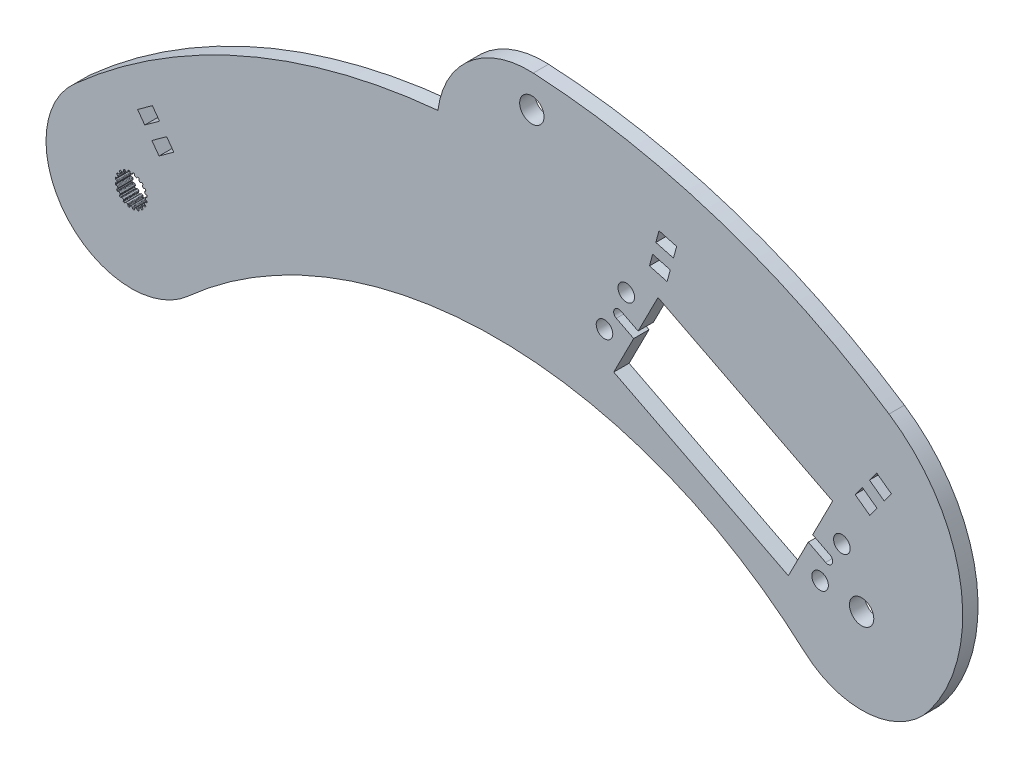
SolidWorks part; units mm, degrees
ref_plane "Front Plane" through (0, 0, 0) normal (0, 0, 1) x (1, 0, 0)
ref_plane "Top Plane" through (0, 0, 0) normal (0, 1, 0) x (1, 0, 0)
ref_plane "Right Plane" through (0, 0, 0) normal (1, 0, 0) x (0, 0, -1)
sketch "Sketch1" plane through (0, 0, 0) normal (0, 0, 1) x (1, 0, 0)
  line L0 (-0.1069, 2.9699) -> (0.1069, 2.9699)
  line L1 (0.3159, 3.2375) -> (0.2537, 3.0575)
  line L2 (-0.2964, 3.2367) -> (-0.2318, 3.0575)
  line L3 (-0.2964, 3.2367) -> (0.3159, 3.2375) construction
  line L4 (0, 3.3252) -> (0, 0) construction
  line L5 (-0.2318, 3.0575) -> (0.2537, 3.0575) construction
  line L6 (-0.4281, 3.3241) -> (0.4281, 3.3263) construction
  line L7 (0.7183, 3.1698) -> (0.7244, 2.9795)
  line L8 (0.816, 2.8576) -> (1.0195, 2.7915)
  line L9 (1.3009, 2.9815) -> (1.1862, 2.8295)
  line L10 (1.6627, 2.7927) -> (1.6097, 2.6099)
  line L11 (1.6591, 2.4655) -> (1.8322, 2.3398)
  line L12 (2.1585, 2.4335) -> (2.0025, 2.3245)
  line L13 (2.4443, 2.1423) -> (2.3374, 1.9847)
  line L14 (2.3398, 1.8322) -> (2.4655, 1.6591)
  line L15 (2.8049, 1.6474) -> (2.6228, 1.5919)
  line L16 (2.9866, 1.2821) -> (2.8363, 1.1653)
  line L17 (2.7915, 1.0195) -> (2.8576, 0.816)
  line L18 (3.1767, 0.7) -> (2.9863, 0.7035)
  line L19 (3.2367, 0.2964) -> (3.0575, 0.2318)
  line L20 (2.9699, 0.1069) -> (2.9699, -0.1069)
  line L21 (3.2375, -0.3159) -> (3.0575, -0.2537)
  line L22 (3.1698, -0.7183) -> (2.9795, -0.7244)
  line L23 (2.8576, -0.816) -> (2.7915, -1.0195)
  line L24 (2.9815, -1.3009) -> (2.8295, -1.1862)
  line L25 (2.7927, -1.6627) -> (2.6099, -1.6097)
  line L26 (2.4655, -1.6591) -> (2.3398, -1.8322)
  line L27 (2.4335, -2.1585) -> (2.3245, -2.0025)
  line L28 (2.1423, -2.4443) -> (1.9847, -2.3374)
  line L29 (1.8322, -2.3398) -> (1.6591, -2.4655)
  line L30 (1.6474, -2.8049) -> (1.5919, -2.6228)
  line L31 (1.2821, -2.9866) -> (1.1653, -2.8363)
  line L32 (1.0195, -2.7915) -> (0.816, -2.8576)
  line L33 (0.7, -3.1767) -> (0.7035, -2.9863)
  line L34 (0.2964, -3.2367) -> (0.2318, -3.0575)
  line L35 (0.1069, -2.9699) -> (-0.1069, -2.9699)
  line L36 (-0.3159, -3.2375) -> (-0.2537, -3.0575)
  line L37 (-0.7183, -3.1698) -> (-0.7244, -2.9795)
  line L38 (-0.816, -2.8576) -> (-1.0195, -2.7915)
  line L39 (-1.3009, -2.9815) -> (-1.1862, -2.8295)
  line L40 (-1.6627, -2.7927) -> (-1.6097, -2.6099)
  line L41 (-1.6591, -2.4655) -> (-1.8322, -2.3398)
  line L42 (-2.1585, -2.4335) -> (-2.0025, -2.3245)
  line L43 (-2.4443, -2.1423) -> (-2.3374, -1.9847)
  line L44 (-2.3398, -1.8322) -> (-2.4655, -1.6591)
  line L45 (-2.8049, -1.6474) -> (-2.6228, -1.5919)
  line L46 (-2.9866, -1.2821) -> (-2.8363, -1.1653)
  line L47 (-2.7915, -1.0195) -> (-2.8576, -0.816)
  line L48 (-3.1767, -0.7) -> (-2.9863, -0.7035)
  line L49 (-3.2367, -0.2964) -> (-3.0575, -0.2318)
  line L50 (-2.9699, -0.1069) -> (-2.9699, 0.1069)
  line L51 (-3.2375, 0.3159) -> (-3.0575, 0.2537)
  line L52 (-3.1698, 0.7183) -> (-2.9795, 0.7244)
  line L53 (-2.8576, 0.816) -> (-2.7915, 1.0195)
  line L54 (-2.9815, 1.3009) -> (-2.8295, 1.1862)
  line L55 (-2.7927, 1.6627) -> (-2.6099, 1.6097)
  line L56 (-2.4655, 1.6591) -> (-2.3398, 1.8322)
  line L57 (-2.4335, 2.1585) -> (-2.3245, 2.0025)
  line L58 (-2.1423, 2.4443) -> (-1.9847, 2.3374)
  line L59 (-1.8322, 2.3398) -> (-1.6591, 2.4655)
  line L60 (-1.6474, 2.8049) -> (-1.5919, 2.6228)
  line L61 (-1.2821, 2.9866) -> (-1.1653, 2.8363)
  line L62 (-1.0195, 2.7915) -> (-0.816, 2.8576)
  line L63 (-0.7, 3.1767) -> (-0.7035, 2.9863)
  line L64 (0.4281, 3.3263) -> (0.62, 3.2938)
  line L65 (1.4351, 3.0312) -> (1.6075, 2.9409)
  line L66 (2.3015, 2.4394) -> (2.4376, 2.3003)
  line L67 (2.9427, 1.6088) -> (3.0291, 1.4344)
  line L68 (3.2958, 0.6207) -> (3.3241, 0.4281)
  line L69 (3.3263, -0.4281) -> (3.2938, -0.62)
  line L70 (3.0312, -1.4351) -> (2.9409, -1.6075)
  line L71 (2.4394, -2.3015) -> (2.3003, -2.4376)
  line L72 (1.6088, -2.9427) -> (1.4344, -3.0291)
  line L73 (0.6207, -3.2958) -> (0.4281, -3.3241)
  line L74 (-0.4281, -3.3263) -> (-0.62, -3.2938)
  line L75 (-1.4351, -3.0312) -> (-1.6075, -2.9409)
  line L76 (-2.3015, -2.4394) -> (-2.4376, -2.3003)
  line L77 (-2.9427, -1.6088) -> (-3.0291, -1.4344)
  line L78 (-3.2958, -0.6207) -> (-3.3241, -0.4281)
  line L79 (-3.3263, 0.4281) -> (-3.2938, 0.62)
  line L80 (-3.0312, 1.4351) -> (-2.9409, 1.6075)
  line L81 (-2.4394, 2.3015) -> (-2.3003, 2.4376)
  line L82 (-1.6088, 2.9427) -> (-1.4344, 3.0291)
  line L83 (-0.6207, 3.2958) -> (-0.4281, 3.3241)
  line L84 (-11.8753, 13.2369) -> (11.8753, -13.2369) construction
  line L85 (164.2753, 13.2369) -> (140.5247, -13.2369) construction
  line L86 (0, 0) -> (152.4, 0) construction
  arc A0 (0.2537, 3.0575) -> (0.1069, 2.9699) centre (0.1283, 3.1009) cw
  arc A1 (-0.2318, 3.0575) -> (-0.1069, 2.9699) centre (-0.1069, 3.1026) ccw
  arc A2 (0.62, 3.2938) -> (0.7183, 3.1698) centre (0.5856, 3.1656) cw
  arc A3 (0.7244, 2.9795) -> (0.816, 2.8576) centre (0.857, 2.9838) ccw
  arc A4 (-0.4281, 3.3241) -> (-0.2964, 3.2367) centre (-0.4213, 3.1916) cw
  arc A5 (0.4281, 3.3263) -> (0.3159, 3.2375) centre (0.4413, 3.1942) ccw
  arc A6 (1.1862, 2.8295) -> (1.0195, 2.7915) centre (1.0802, 2.9095) cw
  arc A7 (1.4351, 3.0312) -> (1.3009, 2.9815) centre (1.4068, 2.9015) ccw
  arc A8 (1.6075, 2.9409) -> (1.6627, 2.7927) centre (1.5352, 2.8297) cw
  arc A9 (1.6097, 2.6099) -> (1.6591, 2.4655) centre (1.7371, 2.5729) ccw
  arc A10 (2.0025, 2.3245) -> (1.8322, 2.3398) centre (1.9264, 2.4332) cw
  arc A11 (2.3015, 2.4394) -> (2.1585, 2.4335) centre (2.2346, 2.3248) ccw
  arc A12 (2.4376, 2.3003) -> (2.4443, 2.1423) centre (2.3345, 2.2168) cw
  arc A13 (2.3374, 1.9847) -> (2.3398, 1.8322) centre (2.4472, 1.9102) ccw
  arc A14 (2.6228, 1.5919) -> (2.4655, 1.6591) centre (2.5841, 1.7189) cw
  arc A15 (2.9427, 1.6088) -> (2.8049, 1.6474) centre (2.8436, 1.5205) ccw
  arc A16 (3.0291, 1.4344) -> (2.9866, 1.2821) centre (2.9052, 1.3869) cw
  arc A17 (2.8363, 1.1653) -> (2.7915, 1.0195) centre (2.9177, 1.0605) ccw
  arc A18 (2.9863, 0.7035) -> (2.8576, 0.816) centre (2.9887, 0.8362) cw
  arc A19 (3.2958, 0.6207) -> (3.1767, 0.7) centre (3.1743, 0.5673) ccw
  arc A20 (3.3241, 0.4281) -> (3.2367, 0.2964) centre (3.1916, 0.4213) cw
  arc A21 (3.0575, 0.2318) -> (2.9699, 0.1069) centre (3.1026, 0.1069) ccw
  arc A22 (3.0575, -0.2537) -> (2.9699, -0.1069) centre (3.1009, -0.1283) cw
  arc A23 (3.3263, -0.4281) -> (3.2375, -0.3159) centre (3.1942, -0.4413) ccw
  arc A24 (3.2938, -0.62) -> (3.1698, -0.7183) centre (3.1656, -0.5856) cw
  arc A25 (2.9795, -0.7244) -> (2.8576, -0.816) centre (2.9838, -0.857) ccw
  arc A26 (2.8295, -1.1862) -> (2.7915, -1.0195) centre (2.9095, -1.0802) cw
  arc A27 (3.0312, -1.4351) -> (2.9815, -1.3009) centre (2.9015, -1.4068) ccw
  arc A28 (2.9409, -1.6075) -> (2.7927, -1.6627) centre (2.8297, -1.5352) cw
  arc A29 (2.6099, -1.6097) -> (2.4655, -1.6591) centre (2.5729, -1.7371) ccw
  arc A30 (2.3245, -2.0025) -> (2.3398, -1.8322) centre (2.4332, -1.9264) cw
  arc A31 (2.4394, -2.3015) -> (2.4335, -2.1585) centre (2.3248, -2.2346) ccw
  arc A32 (2.3003, -2.4376) -> (2.1423, -2.4443) centre (2.2168, -2.3345) cw
  arc A33 (1.9847, -2.3374) -> (1.8322, -2.3398) centre (1.9102, -2.4472) ccw
  arc A34 (1.5919, -2.6228) -> (1.6591, -2.4655) centre (1.7189, -2.5841) cw
  arc A35 (1.6088, -2.9427) -> (1.6474, -2.8049) centre (1.5205, -2.8436) ccw
  arc A36 (1.4344, -3.0291) -> (1.2821, -2.9866) centre (1.3869, -2.9052) cw
  arc A37 (1.1653, -2.8363) -> (1.0195, -2.7915) centre (1.0605, -2.9177) ccw
  arc A38 (0.7035, -2.9863) -> (0.816, -2.8576) centre (0.8362, -2.9887) cw
  arc A39 (0.6207, -3.2958) -> (0.7, -3.1767) centre (0.5673, -3.1743) ccw
  arc A40 (0.4281, -3.3241) -> (0.2964, -3.2367) centre (0.4213, -3.1916) cw
  arc A41 (0.2318, -3.0575) -> (0.1069, -2.9699) centre (0.1069, -3.1026) ccw
  arc A42 (-0.2537, -3.0575) -> (-0.1069, -2.9699) centre (-0.1283, -3.1009) cw
  arc A43 (-0.4281, -3.3263) -> (-0.3159, -3.2375) centre (-0.4413, -3.1942) ccw
  arc A44 (-0.62, -3.2938) -> (-0.7183, -3.1698) centre (-0.5856, -3.1656) cw
  arc A45 (-0.7244, -2.9795) -> (-0.816, -2.8576) centre (-0.857, -2.9838) ccw
  arc A46 (-1.1862, -2.8295) -> (-1.0195, -2.7915) centre (-1.0802, -2.9095) cw
  arc A47 (-1.4351, -3.0312) -> (-1.3009, -2.9815) centre (-1.4068, -2.9015) ccw
  arc A48 (-1.6075, -2.9409) -> (-1.6627, -2.7927) centre (-1.5352, -2.8297) cw
  arc A49 (-1.6097, -2.6099) -> (-1.6591, -2.4655) centre (-1.7371, -2.5729) ccw
  arc A50 (-2.0025, -2.3245) -> (-1.8322, -2.3398) centre (-1.9264, -2.4332) cw
  arc A51 (-2.3015, -2.4394) -> (-2.1585, -2.4335) centre (-2.2346, -2.3248) ccw
  arc A52 (-2.4376, -2.3003) -> (-2.4443, -2.1423) centre (-2.3345, -2.2168) cw
  arc A53 (-2.3374, -1.9847) -> (-2.3398, -1.8322) centre (-2.4472, -1.9102) ccw
  arc A54 (-2.6228, -1.5919) -> (-2.4655, -1.6591) centre (-2.5841, -1.7189) cw
  arc A55 (-2.9427, -1.6088) -> (-2.8049, -1.6474) centre (-2.8436, -1.5205) ccw
  arc A56 (-3.0291, -1.4344) -> (-2.9866, -1.2821) centre (-2.9052, -1.3869) cw
  arc A57 (-2.8363, -1.1653) -> (-2.7915, -1.0195) centre (-2.9177, -1.0605) ccw
  arc A58 (-2.9863, -0.7035) -> (-2.8576, -0.816) centre (-2.9887, -0.8362) cw
  arc A59 (-3.2958, -0.6207) -> (-3.1767, -0.7) centre (-3.1743, -0.5673) ccw
  arc A60 (-3.3241, -0.4281) -> (-3.2367, -0.2964) centre (-3.1916, -0.4213) cw
  arc A61 (-3.0575, -0.2318) -> (-2.9699, -0.1069) centre (-3.1026, -0.1069) ccw
  arc A62 (-3.0575, 0.2537) -> (-2.9699, 0.1069) centre (-3.1009, 0.1283) cw
  arc A63 (-3.3263, 0.4281) -> (-3.2375, 0.3159) centre (-3.1942, 0.4413) ccw
  arc A64 (-3.2938, 0.62) -> (-3.1698, 0.7183) centre (-3.1656, 0.5856) cw
  arc A65 (-2.9795, 0.7244) -> (-2.8576, 0.816) centre (-2.9838, 0.857) ccw
  arc A66 (-2.8295, 1.1862) -> (-2.7915, 1.0195) centre (-2.9095, 1.0802) cw
  arc A67 (-3.0312, 1.4351) -> (-2.9815, 1.3009) centre (-2.9015, 1.4068) ccw
  arc A68 (-2.9409, 1.6075) -> (-2.7927, 1.6627) centre (-2.8297, 1.5352) cw
  arc A69 (-2.6099, 1.6097) -> (-2.4655, 1.6591) centre (-2.5729, 1.7371) ccw
  arc A70 (-2.3245, 2.0025) -> (-2.3398, 1.8322) centre (-2.4332, 1.9264) cw
  arc A71 (-2.4394, 2.3015) -> (-2.4335, 2.1585) centre (-2.3248, 2.2346) ccw
  arc A72 (-2.3003, 2.4376) -> (-2.1423, 2.4443) centre (-2.2168, 2.3345) cw
  arc A73 (-1.9847, 2.3374) -> (-1.8322, 2.3398) centre (-1.9102, 2.4472) ccw
  arc A74 (-1.5919, 2.6228) -> (-1.6591, 2.4655) centre (-1.7189, 2.5841) cw
  arc A75 (-1.6088, 2.9427) -> (-1.6474, 2.8049) centre (-1.5205, 2.8436) ccw
  arc A76 (-1.4344, 3.0291) -> (-1.2821, 2.9866) centre (-1.3869, 2.9052) cw
  arc A77 (-1.1653, 2.8363) -> (-1.0195, 2.7915) centre (-1.0605, 2.9177) ccw
  arc A78 (-0.7035, 2.9863) -> (-0.816, 2.8576) centre (-0.8362, 2.9887) cw
  arc A79 (-0.6207, 3.2958) -> (-0.7, 3.1767) centre (-0.5673, 3.1743) ccw
  circle A80 centre (0, 0) radius 12.7 construction
  arc A81 (-11.8753, 13.2369) -> (164.2753, 13.2369) centre (76.2, -84.9368) cw
  arc A82 (11.8753, -13.2369) -> (140.5247, -13.2369) centre (76.2, -84.9368) cw
  arc A84 (-11.8753, 13.2369) -> (11.8753, -13.2369) centre (0, 0) ccw
  arc A85 (164.2753, 13.2369) -> (140.5247, -13.2369) centre (152.4, 0) cw
  point P14 (0, 2.9699)
  point P26 (0, 0)
  point P247 (0, 0)
  dimension "D4" = 0.1327
  dimension "D8" = 20
  dimension "D9" = 25.4
  dimension "D10" = 131.8914
  dimension "D1" = 2.9699
  dimension "D2" = 0.2139
  dimension "D3" = 0.1904
  dimension "D5" = 0.0877
  dimension "D6" = 0.4855
  dimension "D7" = 0.8563
  dimension "D11" = 35.5662
  dimension "D12" = 152.4
extrude "Boss-Extrude1" add sketch "Sketch1" along normal blind 3.2004
sketch "Sketch2" plane through (0, 0, 3.2004) normal (0, 0, 1) x (1, 0, 0)
  line L0 (132.2879, 12.7254) -> (132.9641, 14.0508) construction
  line L5 (128.1311, 26.252) -> (118.8966, 8.1515) construction
  line L7 (109.9175, 35.5442) -> (146.3447, 16.9598)
  line L13 (109.9175, 35.5442) -> (100.683, 17.4437)
  line L19 (98.7496, 24.2228) -> (103.2942, 33.1305) construction
  line L20 (143.7335, 1.273) -> (148.2781, 10.1807) construction
  line L24 (101.0219, 28.6767) -> (146.0058, 5.7268) construction
  line L30 (100.683, 17.4437) -> (137.1102, -1.1407)
  line L31 (146.3447, 16.9598) -> (137.1102, -1.1407)
  circle A7 centre (103.2942, 33.1305) radius 1.7272
  circle A9 centre (143.7335, 1.273) radius 1.7272
  circle A10 centre (148.2781, 10.1807) radius 1.7272
  circle A11 centre (98.7496, 24.2228) radius 1.7272
  circle A13 centre (132.2879, 12.7254) radius 3.429 construction
  arc A14 (0, 0) -> (152.4, 0) centre (76.2, -84.9368) cw construction
  arc A15 (-11.8753, 13.2369) -> (11.8753, -13.2369) centre (0, 0) ccw construction
  arc A16 (140.5247, -13.2369) -> (164.2753, 13.2369) centre (152.4, 0) ccw construction
  arc A17 (164.2753, 13.2369) -> (-11.8753, 13.2369) centre (76.2, -84.9368) ccw construction
  circle A18 centre (152.4, 0) radius 2.54
  point P0 (132.2879, 12.7254)
  point P1 (99.9946, 26.663)
  point P24 (123.5139, 17.2018)
  dimension "D2" = 15.4
  dimension "D3" = 6.858
  dimension "D5" = 3.4544
  dimension "D10" = 5.08
  dimension "D6" = 2.2606
  dimension "D8" = 20.32
  dimension "D13" = 23.7998
  dimension "D1" = 50.5
  dimension "D4" = 10
  dimension "D7" = 1.4879
  dimension "D9" = 40.894
extrude "Cut-Extrude1" cut sketch "Sketch2" against normal up to surface (3.2004 mm away) up to face at (76.2, 8.6481, 0)
sketch "Sketch3" plane through (0, 0, 3.2004) normal (0, 0, 1) x (1, 0, 0)
  line L0 (146.3447, 16.9598) -> (137.1102, -1.1407) construction
  line L1 (109.9175, 35.5442) -> (100.683, 17.4437) construction
  line L4 (102.1419, 29.2459) -> (105.762, 27.399)
  line L5 (102.1419, 29.2459) -> (101.2184, 27.4358) construction
  line L7 (101.2184, 27.4358) -> (104.8385, 25.5889)
  line L8 (105.762, 27.399) -> (104.8385, 25.5889)
  line L9 (142.1892, 8.8146) -> (145.8093, 6.9677)
  line L10 (142.1892, 8.8146) -> (141.2657, 7.0045)
  line L11 (141.2657, 7.0045) -> (144.8858, 5.1576)
  line L12 (145.8093, 6.9677) -> (144.8858, 5.1576) construction
  arc A6 (145.8093, 6.9677) -> (144.8858, 5.1576) centre (145.3475, 6.0627) cw
  arc A7 (102.1419, 29.2459) -> (101.2184, 27.4358) centre (101.6802, 28.3409) ccw
  point P22 (105.3003, 26.494)
  point P23 (141.7274, 7.9096)
  dimension "D4" = 4.064
  dimension "D5" = 2.032
extrude "Cut-Extrude2" cut sketch "Sketch3" against normal up to surface (3.2004 mm away) up to face at (97.0224, 24.2228, 0)
sketch "Sketch4" plane through (0, 0, 3.2004) normal (0, 0, 1) x (1, 0, 0)
  line L1 (83.5881, 56.2861) -> (152.4, 0) construction
  line L2 (83.5881, 56.2861) -> (83.1655, 46.7705) construction
  line L4 (158.1231, 38.5869) -> (166.6312, -10.6636) construction
  line L5 (83.89, 63.0847) -> (63.9945, 46.3886) construction
  arc A0 (63.9945, 46.3886) -> (83.89, 63.0847) centre (82.9016, 44.0604) cw
  arc A1 (164.2753, 13.2369) -> (-11.8753, 13.2369) centre (76.2, -84.9368) ccw construction
  circle A3 centre (152.4, 0) radius 2.54 construction
  circle A4 centre (83.5881, 56.2861) radius 2.54
  circle A5 centre (152.4, 0) radius 2.54 construction
  arc A6 (83.89, 63.0847) -> (158.1231, 38.5869) centre (76.2, -84.9368) cw
  arc A7 (166.6312, -10.6636) -> (164.2753, 13.2369) centre (152.4, 0) ccw
  arc A8 (164.2753, 13.2369) -> (63.9945, 46.3886) centre (76.2, -84.9368) ccw
  arc A9 (164.2753, 13.2369) -> (-11.8753, 13.2369) centre (76.2, -84.9368) ccw construction
  arc A10 (158.1231, 38.5869) -> (166.6312, -10.6636) centre (139.1275, 9.9453) cw
  arc A11 (140.5247, -13.2369) -> (164.2753, 13.2369) centre (152.4, 0) ccw construction
  dimension "D4" = 49.98
  dimension "D3" = 19.05
  dimension "D1" = 9.525
  dimension "D2" = 88.9
  dimension "D5" = 25.9729
  dimension "D6" = 53.261
extrude "Boss-Extrude2" add sketch "Sketch4" against normal up to surface (3.2004 mm away) up to face at (123.5139, 17.2018, 0)
sketch "Sketch5" plane through (0, 0, 0) normal (0, 0, -1) x (-1, 0, 0)
  line L0 (-111.6319, 45.9923) -> (-110.3049, 41.0887) construction
  line L5 (0, 0) -> (-152.4, 0) construction
  line L6 (-3.6199, 15.3129) -> (-6.599, 11.1981) construction
  line L7 (-7.4632, 14.9596) -> (-2.7557, 11.5514) construction
  line L8 (-156.3207, 24.5097) -> (-153.3199, 20.4107) construction
  line L9 (-109.1295, 44.0381) -> (-112.8073, 43.0429) construction
  line L10 (-156.3574, 21.3349) -> (-153.2832, 23.5854) construction
  line L11 (-113.4708, 45.4947) -> (-109.7931, 46.4899) construction
  line L12 (-113.8025, 46.7206) -> (-110.1248, 47.7159)
  line L13 (-113.8025, 46.7206) -> (-113.139, 44.2688)
  line L14 (-113.139, 44.2688) -> (-109.4613, 45.264)
  line L15 (-110.1248, 47.7159) -> (-109.4613, 45.264)
  line L20 (-112.1438, 40.5911) -> (-108.466, 41.5863) construction
  line L21 (-112.4755, 41.817) -> (-108.7978, 42.8122)
  line L22 (-112.4755, 41.817) -> (-111.812, 39.3652)
  line L23 (-111.812, 39.3652) -> (-108.1343, 40.3604)
  line L24 (-108.7978, 42.8122) -> (-108.1343, 40.3604)
  line L25 (-154.7835, 25.635) -> (-157.8578, 23.3844) construction
  line L26 (-155.5337, 26.6597) -> (-158.608, 24.4092)
  line L27 (-155.5337, 26.6597) -> (-154.0333, 24.6102)
  line L28 (-154.0333, 24.6102) -> (-157.1076, 22.3597)
  line L29 (-158.608, 24.4092) -> (-157.1076, 22.3597)
  line L30 (-154.8571, 19.2854) -> (-151.7828, 21.5359) construction
  line L31 (-155.6073, 20.3101) -> (-152.533, 22.5607)
  line L32 (-155.6073, 20.3101) -> (-154.1069, 18.2606)
  line L33 (-154.1069, 18.2606) -> (-151.0326, 20.5112)
  line L34 (-152.533, 22.5607) -> (-151.0326, 20.5112)
  line L35 (-163.8646, 15.214) -> (-152.4, 0) construction
  line L36 (-2.0769, 14.1957) -> (-5.163, 16.43) construction
  line L37 (-2.8216, 13.167) -> (-5.9077, 15.4013)
  line L38 (-2.8216, 13.167) -> (-1.3321, 15.2244)
  line L39 (-1.3321, 15.2244) -> (-4.4182, 17.4587)
  line L40 (-5.9077, 15.4013) -> (-4.4182, 17.4587)
  line L41 (-5.0559, 10.0809) -> (-8.142, 12.3152) construction
  line L42 (-5.8007, 9.0522) -> (-8.8868, 11.2865)
  line L43 (-5.8007, 9.0522) -> (-4.3112, 11.1096)
  line L44 (-4.3112, 11.1096) -> (-7.3973, 13.3439)
  line L45 (-8.8868, 11.2865) -> (-7.3973, 13.3439)
  line L46 (0, 0) -> (4.7527, 5.2976) construction
  line L47 (8.8586, 1.6141) -> (0.6468, 8.9812) construction
  circle A0 centre (-152.4, 0) radius 2.54 construction
  arc A1 (-163.8646, 15.214) -> (-102.2568, 45.5864) centre (-76.2, -84.9368) cw construction
  arc A4 (11.8753, 13.2369) -> (-164.2753, 13.2369) centre (-76.2, -84.9368) ccw construction
  arc A5 (-31.5472, 27.7651) -> (4.7527, 5.2976) centre (-76.2, -84.9368) cw construction
  arc A6 (-11.8753, -13.2369) -> (11.8753, 13.2369) centre (0, 0) ccw construction
  point P18 (-5.1095, 13.2555)
  point P26 (-154.8203, 22.4602)
  point P27 (-110.9684, 43.5405)
  dimension "D1" = 19.05
  dimension "D2" = 127
  dimension "D3" = 7.1171
  dimension "D4" = 3.81
  dimension "D5" = 2.54
  dimension "D6" = 3.81
  dimension "D7" = 5.08
extrude "Cut-Extrude3" cut sketch "Sketch5" against normal up to surface (3.2004 mm away) up to face at (86.6855, 21.1432, 3.2004)
